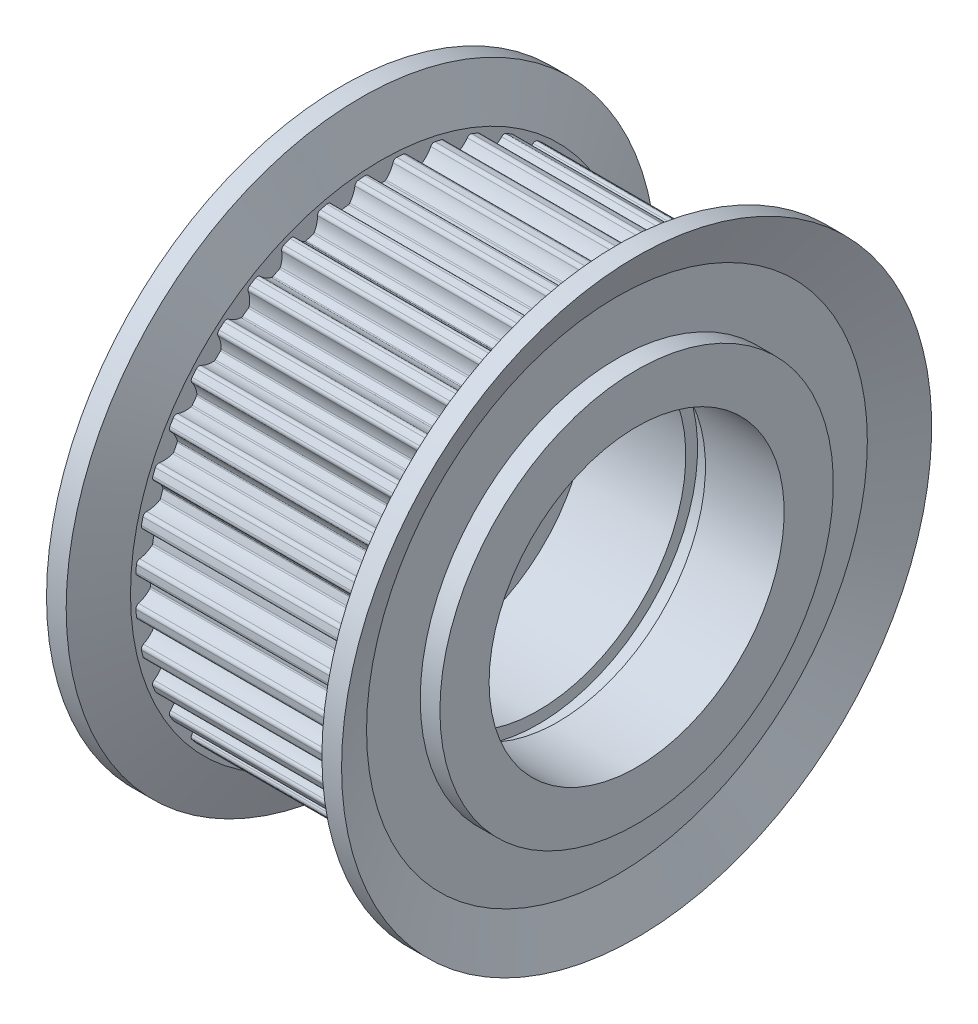
SolidWorks part; units mm, degrees
ref_plane "Front Plane" through (0, 0, 0) normal (0, 0, 1) x (1, 0, 0)
ref_plane "Top Plane" through (0, 0, 0) normal (0, 1, 0) x (1, 0, 0)
ref_plane "Right Plane" through (0, 0, 0) normal (1, 0, 0) x (0, 0, -1)
ref_plane "Plane1" through (0, 0, 0) normal (0, 0, 1) x (1, 0, 0)
sketch "Sketch1" plane through (0, 0, 0) normal (0, 0, 1) x (1, 0, 0)
  line L0 (-7.5, 6.5) -> (-2.5, 6.5)
  line L1 (-2.5, 6.5) -> (-2.5, 7.5)
  line L2 (-2.5, 7.5) -> (2.5, 7.5)
  line L3 (2.5, 7.5) -> (2.5, 8.1)
  line L4 (2.5, 8.1) -> (3.5, 8.1)
  line L5 (3.5, 8.1) -> (3.5, 7.5)
  line L6 (3.5, 7.5) -> (7.5, 7.5)
  line L7 (7.5, 7.5) -> (7.5, 10)
  line L8 (7.5, 10) -> (6.5, 10)
  line L9 (6.5, 10) -> (6.5, 12.73)
  line L10 (6.5, 12.73) -> (7.5, 15)
  line L11 (7.5, 15) -> (6.5, 15)
  line L12 (6.5, 15) -> (5.5, 12.73)
  line L13 (5.5, 12.73) -> (5.5, 12.48)
  line L14 (5.5, 12.48) -> (-5.5, 12.48)
  line L15 (-5.5, 12.48) -> (-5.5, 12.73)
  line L16 (-5.5, 12.73) -> (-6.5, 15)
  line L17 (-6.5, 15) -> (-7.5, 15)
  line L18 (-7.5, 15) -> (-6.5, 12.73)
  line L19 (-6.5, 12.73) -> (-6.5, 10)
  line L20 (-6.5, 10) -> (-7.5, 10)
  line L21 (-7.5, 10) -> (-7.5, 6.5)
  line L22 (15, 0) -> (-15, 0) construction
revolve "Revolve1" add sketch "Sketch1" angle 360 about L22
ref_plane "Plane2" through (5.5, 0, 0) normal (1, 0, 0) x (0, 0, -1)
sketch "Sketch2" plane through (5.5, 0, 0) normal (1, 0, 0) x (0, 0, -1)
  line L0 (0.8092, 12.4537) -> (0.8092, 13.2144)
  line L1 (-0.8092, 13.2144) -> (-0.8092, 12.4537)
  arc A0 (-0.8092, 12.4537) -> (-0.6154, 12.3205) centre (-0.7969, 12.2641) cw
  arc A1 (-0.6154, 12.3205) -> (-0.2549, 11.7455) centre (0.65, 12.7134) ccw
  arc A2 (-0.2549, 11.7455) -> (-0.185, 11.7185) centre (-0.1866, 11.8185) ccw
  arc A3 (-0.185, 11.7185) -> (0.185, 11.7185) centre (0, 0) cw
  arc A4 (0.185, 11.7185) -> (0.2549, 11.7455) centre (0.1866, 11.8185) ccw
  arc A5 (0.2549, 11.7455) -> (0.6154, 12.3205) centre (-0.65, 12.7134) ccw
  arc A6 (0.6154, 12.3205) -> (0.8092, 12.4537) centre (0.7969, 12.2641) cw
  arc A7 (0.8092, 13.2144) -> (-0.8092, 13.2144) centre (0, 0) ccw
extrude "Cut-Extrude1" cut sketch "Sketch2" against normal blind 11
ref_plane "Plane3" through (5.5, 0, 0) normal (1, 0, 0) x (0, 0, -1)
sketch "Sketch3" plane through (5.5, 0, 0) normal (1, 0, 0) x (0, 0, -1)
  line L0 (2.7474, 12.1738) -> (2.8664, 12.9252)
  line L1 (1.268, 13.1783) -> (1.149, 12.427)
  arc A0 (1.149, 12.427) -> (1.3195, 12.2651) centre (1.1315, 12.2378) cw
  arc A1 (1.3195, 12.2651) -> (1.5857, 11.6407) centre (2.6308, 12.4552) ccw
  arc A2 (1.5857, 11.6407) -> (1.6505, 11.6032) centre (1.6646, 11.7022) ccw
  arc A3 (1.6505, 11.6032) -> (2.0159, 11.5453) centre (0, 0) cw
  arc A4 (2.0159, 11.5453) -> (2.0891, 11.561) centre (2.0331, 11.6438) ccw
  arc A5 (2.0891, 11.561) -> (2.5352, 12.0725) centre (1.3468, 12.6586) ccw
  arc A6 (2.5352, 12.0725) -> (2.7474, 12.1738) centre (2.7056, 11.9885) cw
  arc A7 (2.8664, 12.9252) -> (1.268, 13.1783) centre (0, 0) ccw
extrude "Cut-Extrude2" cut sketch "Sketch3" against normal blind 11
ref_plane "Plane4" through (5.5, 0, 0) normal (1, 0, 0) x (0, 0, -1)
sketch "Sketch4" plane through (5.5, 0, 0) normal (1, 0, 0) x (0, 0, -1)
  line L0 (4.618, 11.5942) -> (4.8531, 12.3176)
  line L1 (3.3139, 12.8177) -> (3.0788, 12.0943)
  arc A0 (3.0788, 12.0943) -> (3.222, 11.9076) centre (3.032, 11.9101) cw
  arc A1 (3.222, 11.9076) -> (3.3872, 11.2494) centre (4.5468, 11.8903) ccw
  arc A2 (3.3872, 11.2494) -> (3.4453, 11.2022) centre (3.4747, 11.2977) ccw
  arc A3 (3.4453, 11.2022) -> (3.7972, 11.0878) centre (0, 0) cw
  arc A4 (3.7972, 11.0878) -> (3.8719, 11.0919) centre (3.8296, 11.1824) ccw
  arc A5 (3.8719, 11.0919) -> (4.3925, 11.5273) centre (3.3105, 12.292) ccw
  arc A6 (4.3925, 11.5273) -> (4.618, 11.5942) centre (4.5477, 11.4176) cw
  arc A7 (4.8531, 12.3176) -> (3.3139, 12.8177) centre (0, 0) ccw
extrude "Cut-Extrude3" cut sketch "Sketch4" against normal blind 11
ref_plane "Plane5" through (5.5, 0, 0) normal (1, 0, 0) x (0, 0, -1)
sketch "Sketch5" plane through (5.5, 0, 0) normal (1, 0, 0) x (0, 0, -1)
  line L0 (6.3749, 10.729) -> (6.7202, 11.4068)
  line L1 (5.2783, 12.1415) -> (4.9329, 11.4637)
  arc A0 (4.9329, 11.4637) -> (5.0451, 11.257) centre (4.8578, 11.2892) cw
  arc A1 (5.0451, 11.257) -> (5.1053, 10.581) centre (6.3509, 11.0326) ccw
  arc A2 (5.1053, 10.581) -> (5.1553, 10.5253) centre (5.1993, 10.6151) ccw
  arc A3 (5.1553, 10.5253) -> (5.4849, 10.3573) centre (0, 0) cw
  arc A4 (5.4849, 10.3573) -> (5.5594, 10.3496) centre (5.5317, 10.4457) ccw
  arc A5 (5.5594, 10.3496) -> (6.1417, 10.6982) centre (5.1926, 11.6228) ccw
  arc A6 (6.1417, 10.6982) -> (6.3749, 10.729) centre (6.2778, 10.5657) cw
  arc A7 (6.7202, 11.4068) -> (5.2783, 12.1415) centre (0, 0) ccw
extrude "Cut-Extrude4" cut sketch "Sketch5" against normal blind 11
ref_plane "Plane6" through (5.5, 0, 0) normal (1, 0, 0) x (0, 0, -1)
sketch "Sketch6" plane through (5.5, 0, 0) normal (1, 0, 0) x (0, 0, -1)
  line L0 (7.9748, 9.5997) -> (8.4219, 10.2151)
  line L1 (7.1126, 11.1663) -> (6.6655, 10.5509)
  arc A0 (6.6655, 10.5509) -> (6.7439, 10.3292) centre (6.564, 10.3903) cw
  arc A1 (6.7439, 10.3292) -> (6.6976, 9.6521) centre (7.9986, 9.9033) ccw
  arc A2 (6.6976, 9.6521) -> (6.7383, 9.5892) centre (6.7958, 9.671) ccw
  arc A3 (6.7383, 9.5892) -> (7.0376, 9.3718) centre (0, 0) cw
  arc A4 (7.0376, 9.3718) -> (7.11, 9.3525) centre (7.0977, 9.4517) ccw
  arc A5 (7.11, 9.3525) -> (7.7397, 9.6058) centre (6.9469, 10.6674) ccw
  arc A6 (7.7397, 9.6058) -> (7.9748, 9.5997) centre (7.8534, 9.4535) cw
  arc A7 (8.4219, 10.2151) -> (7.1126, 11.1663) centre (0, 0) ccw
extrude "Cut-Extrude5" cut sketch "Sketch6" against normal blind 11
ref_plane "Plane7" through (5.5, 0, 0) normal (1, 0, 0) x (0, 0, -1)
sketch "Sketch7" plane through (5.5, 0, 0) normal (1, 0, 0) x (0, 0, -1)
  line L0 (9.3783, 8.2339) -> (9.9162, 8.7719)
  line L1 (8.7719, 9.9162) -> (8.2339, 9.3783)
  arc A0 (8.2339, 9.3783) -> (8.2767, 9.1471) centre (8.1086, 9.2355) cw
  arc A1 (8.2767, 9.1471) -> (8.1251, 8.4855) centre (9.4493, 8.5301) ccw
  arc A2 (8.1251, 8.4855) -> (8.1555, 8.4171) centre (8.225, 8.4889) ccw
  arc A3 (8.1555, 8.4171) -> (8.4171, 8.1555) centre (0, 0) cw
  arc A4 (8.4171, 8.1555) -> (8.4855, 8.1251) centre (8.4889, 8.225) ccw
  arc A5 (8.4855, 8.1251) -> (9.1471, 8.2767) centre (8.5301, 9.4493) ccw
  arc A6 (9.1471, 8.2767) -> (9.3783, 8.2339) centre (9.2355, 8.1086) cw
  arc A7 (9.9162, 8.7719) -> (8.7719, 9.9162) centre (0, 0) ccw
extrude "Cut-Extrude6" cut sketch "Sketch7" against normal blind 11
ref_plane "Plane8" through (5.5, 0, 0) normal (1, 0, 0) x (0, 0, -1)
sketch "Sketch8" plane through (5.5, 0, 0) normal (1, 0, 0) x (0, 0, -1)
  line L0 (10.5509, 6.6655) -> (11.1663, 7.1126)
  line L1 (10.2151, 8.4219) -> (9.5997, 7.9748)
  arc A0 (9.5997, 7.9748) -> (9.6058, 7.7397) centre (9.4535, 7.8534) cw
  arc A1 (9.6058, 7.7397) -> (9.3525, 7.11) centre (10.6674, 6.9469) ccw
  arc A2 (9.3525, 7.11) -> (9.3718, 7.0376) centre (9.4517, 7.0977) ccw
  arc A3 (9.3718, 7.0376) -> (9.5892, 6.7383) centre (0, 0) cw
  arc A4 (9.5892, 6.7383) -> (9.6521, 6.6976) centre (9.671, 6.7958) ccw
  arc A5 (9.6521, 6.6976) -> (10.3292, 6.7439) centre (9.9033, 7.9986) ccw
  arc A6 (10.3292, 6.7439) -> (10.5509, 6.6655) centre (10.3903, 6.564) cw
  arc A7 (11.1663, 7.1126) -> (10.2151, 8.4219) centre (0, 0) ccw
extrude "Cut-Extrude7" cut sketch "Sketch8" against normal blind 11
ref_plane "Plane9" through (5.5, 0, 0) normal (1, 0, 0) x (0, 0, -1)
sketch "Sketch9" plane through (5.5, 0, 0) normal (1, 0, 0) x (0, 0, -1)
  line L0 (11.4637, 4.9329) -> (12.1415, 5.2783)
  line L1 (11.4068, 6.7202) -> (10.729, 6.3749)
  arc A0 (10.729, 6.3749) -> (10.6982, 6.1417) centre (10.5657, 6.2778) cw
  arc A1 (10.6982, 6.1417) -> (10.3496, 5.5594) centre (11.6228, 5.1926) ccw
  arc A2 (10.3496, 5.5594) -> (10.3573, 5.4849) centre (10.4457, 5.5317) ccw
  arc A3 (10.3573, 5.4849) -> (10.5253, 5.1553) centre (0, 0) cw
  arc A4 (10.5253, 5.1553) -> (10.581, 5.1053) centre (10.6151, 5.1993) ccw
  arc A5 (10.581, 5.1053) -> (11.257, 5.0451) centre (11.0326, 6.3509) ccw
  arc A6 (11.257, 5.0451) -> (11.4637, 4.9329) centre (11.2892, 4.8578) cw
  arc A7 (12.1415, 5.2783) -> (11.4068, 6.7202) centre (0, 0) ccw
extrude "Cut-Extrude8" cut sketch "Sketch9" against normal blind 11
ref_plane "Plane10" through (5.5, 0, 0) normal (1, 0, 0) x (0, 0, -1)
sketch "Sketch10" plane through (5.5, 0, 0) normal (1, 0, 0) x (0, 0, -1)
  line L0 (12.0943, 3.0788) -> (12.8177, 3.3139)
  line L1 (12.3176, 4.8531) -> (11.5942, 4.618)
  arc A0 (11.5942, 4.618) -> (11.5273, 4.3925) centre (11.4176, 4.5477) cw
  arc A1 (11.5273, 4.3925) -> (11.0919, 3.8719) centre (12.292, 3.3105) ccw
  arc A2 (11.0919, 3.8719) -> (11.0878, 3.7972) centre (11.1824, 3.8296) ccw
  arc A3 (11.0878, 3.7972) -> (11.2022, 3.4453) centre (0, 0) cw
  arc A4 (11.2022, 3.4453) -> (11.2494, 3.3872) centre (11.2977, 3.4747) ccw
  arc A5 (11.2494, 3.3872) -> (11.9076, 3.222) centre (11.8903, 4.5468) ccw
  arc A6 (11.9076, 3.222) -> (12.0943, 3.0788) centre (11.9101, 3.032) cw
  arc A7 (12.8177, 3.3139) -> (12.3176, 4.8531) centre (0, 0) ccw
extrude "Cut-Extrude9" cut sketch "Sketch10" against normal blind 11
ref_plane "Plane11" through (5.5, 0, 0) normal (1, 0, 0) x (0, 0, -1)
sketch "Sketch11" plane through (5.5, 0, 0) normal (1, 0, 0) x (0, 0, -1)
  line L0 (12.427, 1.149) -> (13.1783, 1.268)
  line L1 (12.9252, 2.8664) -> (12.1738, 2.7474)
  arc A0 (12.1738, 2.7474) -> (12.0725, 2.5352) centre (11.9885, 2.7056) cw
  arc A1 (12.0725, 2.5352) -> (11.561, 2.0891) centre (12.6586, 1.3468) ccw
  arc A2 (11.561, 2.0891) -> (11.5453, 2.0159) centre (11.6438, 2.0331) ccw
  arc A3 (11.5453, 2.0159) -> (11.6032, 1.6505) centre (0, 0) cw
  arc A4 (11.6032, 1.6505) -> (11.6407, 1.5857) centre (11.7022, 1.6646) ccw
  arc A5 (11.6407, 1.5857) -> (12.2651, 1.3195) centre (12.4552, 2.6308) ccw
  arc A6 (12.2651, 1.3195) -> (12.427, 1.149) centre (12.2378, 1.1315) cw
  arc A7 (13.1783, 1.268) -> (12.9252, 2.8664) centre (0, 0) ccw
extrude "Cut-Extrude10" cut sketch "Sketch11" against normal blind 11
ref_plane "Plane12" through (5.5, 0, 0) normal (1, 0, 0) x (0, 0, -1)
sketch "Sketch12" plane through (5.5, 0, 0) normal (1, 0, 0) x (0, 0, -1)
  line L0 (12.4537, -0.8092) -> (13.2144, -0.8092)
  line L1 (13.2144, 0.8092) -> (12.4537, 0.8092)
  arc A0 (12.4537, 0.8092) -> (12.3205, 0.6154) centre (12.2641, 0.7969) cw
  arc A1 (12.3205, 0.6154) -> (11.7455, 0.2549) centre (12.7134, -0.65) ccw
  arc A2 (11.7455, 0.2549) -> (11.7185, 0.185) centre (11.8185, 0.1866) ccw
  arc A3 (11.7185, 0.185) -> (11.7185, -0.185) centre (0, 0) cw
  arc A4 (11.7185, -0.185) -> (11.7455, -0.2549) centre (11.8185, -0.1866) ccw
  arc A5 (11.7455, -0.2549) -> (12.3205, -0.6154) centre (12.7134, 0.65) ccw
  arc A6 (12.3205, -0.6154) -> (12.4537, -0.8092) centre (12.2641, -0.7969) cw
  arc A7 (13.2144, -0.8092) -> (13.2144, 0.8092) centre (0, 0) ccw
extrude "Cut-Extrude11" cut sketch "Sketch12" against normal blind 11
ref_plane "Plane13" through (5.5, 0, 0) normal (1, 0, 0) x (0, 0, -1)
sketch "Sketch13" plane through (5.5, 0, 0) normal (1, 0, 0) x (0, 0, -1)
  line L0 (12.1738, -2.7474) -> (12.9252, -2.8664)
  line L1 (13.1783, -1.268) -> (12.427, -1.149)
  arc A0 (12.427, -1.149) -> (12.2651, -1.3195) centre (12.2378, -1.1315) cw
  arc A1 (12.2651, -1.3195) -> (11.6407, -1.5857) centre (12.4552, -2.6308) ccw
  arc A2 (11.6407, -1.5857) -> (11.6032, -1.6505) centre (11.7022, -1.6646) ccw
  arc A3 (11.6032, -1.6505) -> (11.5453, -2.0159) centre (0, 0) cw
  arc A4 (11.5453, -2.0159) -> (11.561, -2.0891) centre (11.6438, -2.0331) ccw
  arc A5 (11.561, -2.0891) -> (12.0725, -2.5352) centre (12.6586, -1.3468) ccw
  arc A6 (12.0725, -2.5352) -> (12.1738, -2.7474) centre (11.9885, -2.7056) cw
  arc A7 (12.9252, -2.8664) -> (13.1783, -1.268) centre (0, 0) ccw
extrude "Cut-Extrude12" cut sketch "Sketch13" against normal blind 11
ref_plane "Plane14" through (5.5, 0, 0) normal (1, 0, 0) x (0, 0, -1)
sketch "Sketch14" plane through (5.5, 0, 0) normal (1, 0, 0) x (0, 0, -1)
  line L0 (11.5942, -4.618) -> (12.3176, -4.8531)
  line L1 (12.8177, -3.3139) -> (12.0943, -3.0788)
  arc A0 (12.0943, -3.0788) -> (11.9076, -3.222) centre (11.9101, -3.032) cw
  arc A1 (11.9076, -3.222) -> (11.2494, -3.3872) centre (11.8903, -4.5468) ccw
  arc A2 (11.2494, -3.3872) -> (11.2022, -3.4453) centre (11.2977, -3.4747) ccw
  arc A3 (11.2022, -3.4453) -> (11.0878, -3.7972) centre (0, 0) cw
  arc A4 (11.0878, -3.7972) -> (11.0919, -3.8719) centre (11.1824, -3.8296) ccw
  arc A5 (11.0919, -3.8719) -> (11.5273, -4.3925) centre (12.292, -3.3105) ccw
  arc A6 (11.5273, -4.3925) -> (11.5942, -4.618) centre (11.4176, -4.5477) cw
  arc A7 (12.3176, -4.8531) -> (12.8177, -3.3139) centre (0, 0) ccw
extrude "Cut-Extrude13" cut sketch "Sketch14" against normal blind 11
ref_plane "Plane15" through (5.5, 0, 0) normal (1, 0, 0) x (0, 0, -1)
sketch "Sketch15" plane through (5.5, 0, 0) normal (1, 0, 0) x (0, 0, -1)
  line L0 (10.729, -6.3749) -> (11.4068, -6.7202)
  line L1 (12.1415, -5.2783) -> (11.4637, -4.9329)
  arc A0 (11.4637, -4.9329) -> (11.257, -5.0451) centre (11.2892, -4.8578) cw
  arc A1 (11.257, -5.0451) -> (10.581, -5.1053) centre (11.0326, -6.3509) ccw
  arc A2 (10.581, -5.1053) -> (10.5253, -5.1553) centre (10.6151, -5.1993) ccw
  arc A3 (10.5253, -5.1553) -> (10.3573, -5.4849) centre (0, 0) cw
  arc A4 (10.3573, -5.4849) -> (10.3496, -5.5594) centre (10.4457, -5.5317) ccw
  arc A5 (10.3496, -5.5594) -> (10.6982, -6.1417) centre (11.6228, -5.1926) ccw
  arc A6 (10.6982, -6.1417) -> (10.729, -6.3749) centre (10.5657, -6.2778) cw
  arc A7 (11.4068, -6.7202) -> (12.1415, -5.2783) centre (0, 0) ccw
extrude "Cut-Extrude14" cut sketch "Sketch15" against normal blind 11
ref_plane "Plane16" through (5.5, 0, 0) normal (1, 0, 0) x (0, 0, -1)
sketch "Sketch16" plane through (5.5, 0, 0) normal (1, 0, 0) x (0, 0, -1)
  line L0 (9.5997, -7.9748) -> (10.2151, -8.4219)
  line L1 (11.1663, -7.1126) -> (10.5509, -6.6655)
  arc A0 (10.5509, -6.6655) -> (10.3292, -6.7439) centre (10.3903, -6.564) cw
  arc A1 (10.3292, -6.7439) -> (9.6521, -6.6976) centre (9.9033, -7.9986) ccw
  arc A2 (9.6521, -6.6976) -> (9.5892, -6.7383) centre (9.671, -6.7958) ccw
  arc A3 (9.5892, -6.7383) -> (9.3718, -7.0376) centre (0, 0) cw
  arc A4 (9.3718, -7.0376) -> (9.3525, -7.11) centre (9.4517, -7.0977) ccw
  arc A5 (9.3525, -7.11) -> (9.6058, -7.7397) centre (10.6674, -6.9469) ccw
  arc A6 (9.6058, -7.7397) -> (9.5997, -7.9748) centre (9.4535, -7.8534) cw
  arc A7 (10.2151, -8.4219) -> (11.1663, -7.1126) centre (0, 0) ccw
extrude "Cut-Extrude15" cut sketch "Sketch16" against normal blind 11
ref_plane "Plane17" through (5.5, 0, 0) normal (1, 0, 0) x (0, 0, -1)
sketch "Sketch17" plane through (5.5, 0, 0) normal (1, 0, 0) x (0, 0, -1)
  line L0 (8.2339, -9.3783) -> (8.7719, -9.9162)
  line L1 (9.9162, -8.7719) -> (9.3783, -8.2339)
  arc A0 (9.3783, -8.2339) -> (9.1471, -8.2767) centre (9.2355, -8.1086) cw
  arc A1 (9.1471, -8.2767) -> (8.4855, -8.1251) centre (8.5301, -9.4493) ccw
  arc A2 (8.4855, -8.1251) -> (8.4171, -8.1555) centre (8.4889, -8.225) ccw
  arc A3 (8.4171, -8.1555) -> (8.1555, -8.4171) centre (0, 0) cw
  arc A4 (8.1555, -8.4171) -> (8.1251, -8.4855) centre (8.225, -8.4889) ccw
  arc A5 (8.1251, -8.4855) -> (8.2767, -9.1471) centre (9.4493, -8.5301) ccw
  arc A6 (8.2767, -9.1471) -> (8.2339, -9.3783) centre (8.1086, -9.2355) cw
  arc A7 (8.7719, -9.9162) -> (9.9162, -8.7719) centre (0, 0) ccw
extrude "Cut-Extrude16" cut sketch "Sketch17" against normal blind 11
ref_plane "Plane18" through (5.5, 0, 0) normal (1, 0, 0) x (0, 0, -1)
sketch "Sketch18" plane through (5.5, 0, 0) normal (1, 0, 0) x (0, 0, -1)
  line L0 (6.6655, -10.5509) -> (7.1126, -11.1663)
  line L1 (8.4219, -10.2151) -> (7.9748, -9.5997)
  arc A0 (7.9748, -9.5997) -> (7.7397, -9.6058) centre (7.8534, -9.4535) cw
  arc A1 (7.7397, -9.6058) -> (7.11, -9.3525) centre (6.9469, -10.6674) ccw
  arc A2 (7.11, -9.3525) -> (7.0376, -9.3718) centre (7.0977, -9.4517) ccw
  arc A3 (7.0376, -9.3718) -> (6.7383, -9.5892) centre (0, 0) cw
  arc A4 (6.7383, -9.5892) -> (6.6976, -9.6521) centre (6.7958, -9.671) ccw
  arc A5 (6.6976, -9.6521) -> (6.7439, -10.3292) centre (7.9986, -9.9033) ccw
  arc A6 (6.7439, -10.3292) -> (6.6655, -10.5509) centre (6.564, -10.3903) cw
  arc A7 (7.1126, -11.1663) -> (8.4219, -10.2151) centre (0, 0) ccw
extrude "Cut-Extrude17" cut sketch "Sketch18" against normal blind 11
ref_plane "Plane19" through (5.5, 0, 0) normal (1, 0, 0) x (0, 0, -1)
sketch "Sketch19" plane through (5.5, 0, 0) normal (1, 0, 0) x (0, 0, -1)
  line L0 (4.9329, -11.4637) -> (5.2783, -12.1415)
  line L1 (6.7202, -11.4068) -> (6.3749, -10.729)
  arc A0 (6.3749, -10.729) -> (6.1417, -10.6982) centre (6.2778, -10.5657) cw
  arc A1 (6.1417, -10.6982) -> (5.5594, -10.3496) centre (5.1926, -11.6228) ccw
  arc A2 (5.5594, -10.3496) -> (5.4849, -10.3573) centre (5.5317, -10.4457) ccw
  arc A3 (5.4849, -10.3573) -> (5.1553, -10.5253) centre (0, 0) cw
  arc A4 (5.1553, -10.5253) -> (5.1053, -10.581) centre (5.1993, -10.6151) ccw
  arc A5 (5.1053, -10.581) -> (5.0451, -11.257) centre (6.3509, -11.0326) ccw
  arc A6 (5.0451, -11.257) -> (4.9329, -11.4637) centre (4.8578, -11.2892) cw
  arc A7 (5.2783, -12.1415) -> (6.7202, -11.4068) centre (0, 0) ccw
extrude "Cut-Extrude18" cut sketch "Sketch19" against normal blind 11
ref_plane "Plane20" through (5.5, 0, 0) normal (1, 0, 0) x (0, 0, -1)
sketch "Sketch20" plane through (5.5, 0, 0) normal (1, 0, 0) x (0, 0, -1)
  line L0 (3.0788, -12.0943) -> (3.3139, -12.8177)
  line L1 (4.8531, -12.3176) -> (4.618, -11.5942)
  arc A0 (4.618, -11.5942) -> (4.3925, -11.5273) centre (4.5477, -11.4176) cw
  arc A1 (4.3925, -11.5273) -> (3.8719, -11.0919) centre (3.3105, -12.292) ccw
  arc A2 (3.8719, -11.0919) -> (3.7972, -11.0878) centre (3.8296, -11.1824) ccw
  arc A3 (3.7972, -11.0878) -> (3.4453, -11.2022) centre (0, 0) cw
  arc A4 (3.4453, -11.2022) -> (3.3872, -11.2494) centre (3.4747, -11.2977) ccw
  arc A5 (3.3872, -11.2494) -> (3.222, -11.9076) centre (4.5468, -11.8903) ccw
  arc A6 (3.222, -11.9076) -> (3.0788, -12.0943) centre (3.032, -11.9101) cw
  arc A7 (3.3139, -12.8177) -> (4.8531, -12.3176) centre (0, 0) ccw
extrude "Cut-Extrude19" cut sketch "Sketch20" against normal blind 11
ref_plane "Plane21" through (5.5, 0, 0) normal (1, 0, 0) x (0, 0, -1)
sketch "Sketch21" plane through (5.5, 0, 0) normal (1, 0, 0) x (0, 0, -1)
  line L0 (1.149, -12.427) -> (1.268, -13.1783)
  line L1 (2.8664, -12.9252) -> (2.7474, -12.1738)
  arc A0 (2.7474, -12.1738) -> (2.5352, -12.0725) centre (2.7056, -11.9885) cw
  arc A1 (2.5352, -12.0725) -> (2.0891, -11.561) centre (1.3468, -12.6586) ccw
  arc A2 (2.0891, -11.561) -> (2.0159, -11.5453) centre (2.0331, -11.6438) ccw
  arc A3 (2.0159, -11.5453) -> (1.6505, -11.6032) centre (0, 0) cw
  arc A4 (1.6505, -11.6032) -> (1.5857, -11.6407) centre (1.6646, -11.7022) ccw
  arc A5 (1.5857, -11.6407) -> (1.3195, -12.2651) centre (2.6308, -12.4552) ccw
  arc A6 (1.3195, -12.2651) -> (1.149, -12.427) centre (1.1315, -12.2378) cw
  arc A7 (1.268, -13.1783) -> (2.8664, -12.9252) centre (0, 0) ccw
extrude "Cut-Extrude20" cut sketch "Sketch21" against normal blind 11
ref_plane "Plane22" through (5.5, 0, 0) normal (1, 0, 0) x (0, 0, -1)
sketch "Sketch22" plane through (5.5, 0, 0) normal (1, 0, 0) x (0, 0, -1)
  line L0 (-0.8092, -12.4537) -> (-0.8092, -13.2144)
  line L1 (0.8092, -13.2144) -> (0.8092, -12.4537)
  arc A0 (0.8092, -12.4537) -> (0.6154, -12.3205) centre (0.7969, -12.2641) cw
  arc A1 (0.6154, -12.3205) -> (0.2549, -11.7455) centre (-0.65, -12.7134) ccw
  arc A2 (0.2549, -11.7455) -> (0.185, -11.7185) centre (0.1866, -11.8185) ccw
  arc A3 (0.185, -11.7185) -> (-0.185, -11.7185) centre (0, 0) cw
  arc A4 (-0.185, -11.7185) -> (-0.2549, -11.7455) centre (-0.1866, -11.8185) ccw
  arc A5 (-0.2549, -11.7455) -> (-0.6154, -12.3205) centre (0.65, -12.7134) ccw
  arc A6 (-0.6154, -12.3205) -> (-0.8092, -12.4537) centre (-0.7969, -12.2641) cw
  arc A7 (-0.8092, -13.2144) -> (0.8092, -13.2144) centre (0, 0) ccw
extrude "Cut-Extrude21" cut sketch "Sketch22" against normal blind 11
ref_plane "Plane23" through (5.5, 0, 0) normal (1, 0, 0) x (0, 0, -1)
sketch "Sketch23" plane through (5.5, 0, 0) normal (1, 0, 0) x (0, 0, -1)
  line L0 (-2.7474, -12.1738) -> (-2.8664, -12.9252)
  line L1 (-1.268, -13.1783) -> (-1.149, -12.427)
  arc A0 (-1.149, -12.427) -> (-1.3195, -12.2651) centre (-1.1315, -12.2378) cw
  arc A1 (-1.3195, -12.2651) -> (-1.5857, -11.6407) centre (-2.6308, -12.4552) ccw
  arc A2 (-1.5857, -11.6407) -> (-1.6505, -11.6032) centre (-1.6646, -11.7022) ccw
  arc A3 (-1.6505, -11.6032) -> (-2.0159, -11.5453) centre (0, 0) cw
  arc A4 (-2.0159, -11.5453) -> (-2.0891, -11.561) centre (-2.0331, -11.6438) ccw
  arc A5 (-2.0891, -11.561) -> (-2.5352, -12.0725) centre (-1.3468, -12.6586) ccw
  arc A6 (-2.5352, -12.0725) -> (-2.7474, -12.1738) centre (-2.7056, -11.9885) cw
  arc A7 (-2.8664, -12.9252) -> (-1.268, -13.1783) centre (0, 0) ccw
extrude "Cut-Extrude22" cut sketch "Sketch23" against normal blind 11
ref_plane "Plane24" through (5.5, 0, 0) normal (1, 0, 0) x (0, 0, -1)
sketch "Sketch24" plane through (5.5, 0, 0) normal (1, 0, 0) x (0, 0, -1)
  line L0 (-4.618, -11.5942) -> (-4.8531, -12.3176)
  line L1 (-3.3139, -12.8177) -> (-3.0788, -12.0943)
  arc A0 (-3.0788, -12.0943) -> (-3.222, -11.9076) centre (-3.032, -11.9101) cw
  arc A1 (-3.222, -11.9076) -> (-3.3872, -11.2494) centre (-4.5468, -11.8903) ccw
  arc A2 (-3.3872, -11.2494) -> (-3.4453, -11.2022) centre (-3.4747, -11.2977) ccw
  arc A3 (-3.4453, -11.2022) -> (-3.7972, -11.0878) centre (0, 0) cw
  arc A4 (-3.7972, -11.0878) -> (-3.8719, -11.0919) centre (-3.8296, -11.1824) ccw
  arc A5 (-3.8719, -11.0919) -> (-4.3925, -11.5273) centre (-3.3105, -12.292) ccw
  arc A6 (-4.3925, -11.5273) -> (-4.618, -11.5942) centre (-4.5477, -11.4176) cw
  arc A7 (-4.8531, -12.3176) -> (-3.3139, -12.8177) centre (0, 0) ccw
extrude "Cut-Extrude23" cut sketch "Sketch24" against normal blind 11
ref_plane "Plane25" through (5.5, 0, 0) normal (1, 0, 0) x (0, 0, -1)
sketch "Sketch25" plane through (5.5, 0, 0) normal (1, 0, 0) x (0, 0, -1)
  line L0 (-6.3749, -10.729) -> (-6.7202, -11.4068)
  line L1 (-5.2783, -12.1415) -> (-4.9329, -11.4637)
  arc A0 (-4.9329, -11.4637) -> (-5.0451, -11.257) centre (-4.8578, -11.2892) cw
  arc A1 (-5.0451, -11.257) -> (-5.1053, -10.581) centre (-6.3509, -11.0326) ccw
  arc A2 (-5.1053, -10.581) -> (-5.1553, -10.5253) centre (-5.1993, -10.6151) ccw
  arc A3 (-5.1553, -10.5253) -> (-5.4849, -10.3573) centre (0, 0) cw
  arc A4 (-5.4849, -10.3573) -> (-5.5594, -10.3496) centre (-5.5317, -10.4457) ccw
  arc A5 (-5.5594, -10.3496) -> (-6.1417, -10.6982) centre (-5.1926, -11.6228) ccw
  arc A6 (-6.1417, -10.6982) -> (-6.3749, -10.729) centre (-6.2778, -10.5657) cw
  arc A7 (-6.7202, -11.4068) -> (-5.2783, -12.1415) centre (0, 0) ccw
extrude "Cut-Extrude24" cut sketch "Sketch25" against normal blind 11
ref_plane "Plane26" through (5.5, 0, 0) normal (1, 0, 0) x (0, 0, -1)
sketch "Sketch26" plane through (5.5, 0, 0) normal (1, 0, 0) x (0, 0, -1)
  line L0 (-7.9748, -9.5997) -> (-8.4219, -10.2151)
  line L1 (-7.1126, -11.1663) -> (-6.6655, -10.5509)
  arc A0 (-6.6655, -10.5509) -> (-6.7439, -10.3292) centre (-6.564, -10.3903) cw
  arc A1 (-6.7439, -10.3292) -> (-6.6976, -9.6521) centre (-7.9986, -9.9033) ccw
  arc A2 (-6.6976, -9.6521) -> (-6.7383, -9.5892) centre (-6.7958, -9.671) ccw
  arc A3 (-6.7383, -9.5892) -> (-7.0376, -9.3718) centre (0, 0) cw
  arc A4 (-7.0376, -9.3718) -> (-7.11, -9.3525) centre (-7.0977, -9.4517) ccw
  arc A5 (-7.11, -9.3525) -> (-7.7397, -9.6058) centre (-6.9469, -10.6674) ccw
  arc A6 (-7.7397, -9.6058) -> (-7.9748, -9.5997) centre (-7.8534, -9.4535) cw
  arc A7 (-8.4219, -10.2151) -> (-7.1126, -11.1663) centre (0, 0) ccw
extrude "Cut-Extrude25" cut sketch "Sketch26" against normal blind 11
ref_plane "Plane27" through (5.5, 0, 0) normal (1, 0, 0) x (0, 0, -1)
sketch "Sketch27" plane through (5.5, 0, 0) normal (1, 0, 0) x (0, 0, -1)
  line L0 (-9.3783, -8.2339) -> (-9.9162, -8.7719)
  line L1 (-8.7719, -9.9162) -> (-8.2339, -9.3783)
  arc A0 (-8.2339, -9.3783) -> (-8.2767, -9.1471) centre (-8.1086, -9.2355) cw
  arc A1 (-8.2767, -9.1471) -> (-8.1251, -8.4855) centre (-9.4493, -8.5301) ccw
  arc A2 (-8.1251, -8.4855) -> (-8.1555, -8.4171) centre (-8.225, -8.4889) ccw
  arc A3 (-8.1555, -8.4171) -> (-8.4171, -8.1555) centre (0, 0) cw
  arc A4 (-8.4171, -8.1555) -> (-8.4855, -8.1251) centre (-8.4889, -8.225) ccw
  arc A5 (-8.4855, -8.1251) -> (-9.1471, -8.2767) centre (-8.5301, -9.4493) ccw
  arc A6 (-9.1471, -8.2767) -> (-9.3783, -8.2339) centre (-9.2355, -8.1086) cw
  arc A7 (-9.9162, -8.7719) -> (-8.7719, -9.9162) centre (0, 0) ccw
extrude "Cut-Extrude26" cut sketch "Sketch27" against normal blind 11
ref_plane "Plane28" through (5.5, 0, 0) normal (1, 0, 0) x (0, 0, -1)
sketch "Sketch28" plane through (5.5, 0, 0) normal (1, 0, 0) x (0, 0, -1)
  line L0 (-10.5509, -6.6655) -> (-11.1663, -7.1126)
  line L1 (-10.2151, -8.4219) -> (-9.5997, -7.9748)
  arc A0 (-9.5997, -7.9748) -> (-9.6058, -7.7397) centre (-9.4535, -7.8534) cw
  arc A1 (-9.6058, -7.7397) -> (-9.3525, -7.11) centre (-10.6674, -6.9469) ccw
  arc A2 (-9.3525, -7.11) -> (-9.3718, -7.0376) centre (-9.4517, -7.0977) ccw
  arc A3 (-9.3718, -7.0376) -> (-9.5892, -6.7383) centre (0, 0) cw
  arc A4 (-9.5892, -6.7383) -> (-9.6521, -6.6976) centre (-9.671, -6.7958) ccw
  arc A5 (-9.6521, -6.6976) -> (-10.3292, -6.7439) centre (-9.9033, -7.9986) ccw
  arc A6 (-10.3292, -6.7439) -> (-10.5509, -6.6655) centre (-10.3903, -6.564) cw
  arc A7 (-11.1663, -7.1126) -> (-10.2151, -8.4219) centre (0, 0) ccw
extrude "Cut-Extrude27" cut sketch "Sketch28" against normal blind 11
ref_plane "Plane29" through (5.5, 0, 0) normal (1, 0, 0) x (0, 0, -1)
sketch "Sketch29" plane through (5.5, 0, 0) normal (1, 0, 0) x (0, 0, -1)
  line L0 (-11.4637, -4.9329) -> (-12.1415, -5.2783)
  line L1 (-11.4068, -6.7202) -> (-10.729, -6.3749)
  arc A0 (-10.729, -6.3749) -> (-10.6982, -6.1417) centre (-10.5657, -6.2778) cw
  arc A1 (-10.6982, -6.1417) -> (-10.3496, -5.5594) centre (-11.6228, -5.1926) ccw
  arc A2 (-10.3496, -5.5594) -> (-10.3573, -5.4849) centre (-10.4457, -5.5317) ccw
  arc A3 (-10.3573, -5.4849) -> (-10.5253, -5.1553) centre (0, 0) cw
  arc A4 (-10.5253, -5.1553) -> (-10.581, -5.1053) centre (-10.6151, -5.1993) ccw
  arc A5 (-10.581, -5.1053) -> (-11.257, -5.0451) centre (-11.0326, -6.3509) ccw
  arc A6 (-11.257, -5.0451) -> (-11.4637, -4.9329) centre (-11.2892, -4.8578) cw
  arc A7 (-12.1415, -5.2783) -> (-11.4068, -6.7202) centre (0, 0) ccw
extrude "Cut-Extrude28" cut sketch "Sketch29" against normal blind 11
ref_plane "Plane30" through (5.5, 0, 0) normal (1, 0, 0) x (0, 0, -1)
sketch "Sketch30" plane through (5.5, 0, 0) normal (1, 0, 0) x (0, 0, -1)
  line L0 (-12.0943, -3.0788) -> (-12.8177, -3.3139)
  line L1 (-12.3176, -4.8531) -> (-11.5942, -4.618)
  arc A0 (-11.5942, -4.618) -> (-11.5273, -4.3925) centre (-11.4176, -4.5477) cw
  arc A1 (-11.5273, -4.3925) -> (-11.0919, -3.8719) centre (-12.292, -3.3105) ccw
  arc A2 (-11.0919, -3.8719) -> (-11.0878, -3.7972) centre (-11.1824, -3.8296) ccw
  arc A3 (-11.0878, -3.7972) -> (-11.2022, -3.4453) centre (0, 0) cw
  arc A4 (-11.2022, -3.4453) -> (-11.2494, -3.3872) centre (-11.2977, -3.4747) ccw
  arc A5 (-11.2494, -3.3872) -> (-11.9076, -3.222) centre (-11.8903, -4.5468) ccw
  arc A6 (-11.9076, -3.222) -> (-12.0943, -3.0788) centre (-11.9101, -3.032) cw
  arc A7 (-12.8177, -3.3139) -> (-12.3176, -4.8531) centre (0, 0) ccw
extrude "Cut-Extrude29" cut sketch "Sketch30" against normal blind 11
ref_plane "Plane31" through (5.5, 0, 0) normal (1, 0, 0) x (0, 0, -1)
sketch "Sketch31" plane through (5.5, 0, 0) normal (1, 0, 0) x (0, 0, -1)
  line L0 (-12.427, -1.149) -> (-13.1783, -1.268)
  line L1 (-12.9252, -2.8664) -> (-12.1738, -2.7474)
  arc A0 (-12.1738, -2.7474) -> (-12.0725, -2.5352) centre (-11.9885, -2.7056) cw
  arc A1 (-12.0725, -2.5352) -> (-11.561, -2.0891) centre (-12.6586, -1.3468) ccw
  arc A2 (-11.561, -2.0891) -> (-11.5453, -2.0159) centre (-11.6438, -2.0331) ccw
  arc A3 (-11.5453, -2.0159) -> (-11.6032, -1.6505) centre (0, 0) cw
  arc A4 (-11.6032, -1.6505) -> (-11.6407, -1.5857) centre (-11.7022, -1.6646) ccw
  arc A5 (-11.6407, -1.5857) -> (-12.2651, -1.3195) centre (-12.4552, -2.6308) ccw
  arc A6 (-12.2651, -1.3195) -> (-12.427, -1.149) centre (-12.2378, -1.1315) cw
  arc A7 (-13.1783, -1.268) -> (-12.9252, -2.8664) centre (0, 0) ccw
extrude "Cut-Extrude30" cut sketch "Sketch31" against normal blind 11
ref_plane "Plane32" through (5.5, 0, 0) normal (1, 0, 0) x (0, 0, -1)
sketch "Sketch32" plane through (5.5, 0, 0) normal (1, 0, 0) x (0, 0, -1)
  line L0 (-12.4537, 0.8092) -> (-13.2144, 0.8092)
  line L1 (-13.2144, -0.8092) -> (-12.4537, -0.8092)
  arc A0 (-12.4537, -0.8092) -> (-12.3205, -0.6154) centre (-12.2641, -0.7969) cw
  arc A1 (-12.3205, -0.6154) -> (-11.7455, -0.2549) centre (-12.7134, 0.65) ccw
  arc A2 (-11.7455, -0.2549) -> (-11.7185, -0.185) centre (-11.8185, -0.1866) ccw
  arc A3 (-11.7185, -0.185) -> (-11.7185, 0.185) centre (0, 0) cw
  arc A4 (-11.7185, 0.185) -> (-11.7455, 0.2549) centre (-11.8185, 0.1866) ccw
  arc A5 (-11.7455, 0.2549) -> (-12.3205, 0.6154) centre (-12.7134, -0.65) ccw
  arc A6 (-12.3205, 0.6154) -> (-12.4537, 0.8092) centre (-12.2641, 0.7969) cw
  arc A7 (-13.2144, 0.8092) -> (-13.2144, -0.8092) centre (0, 0) ccw
extrude "Cut-Extrude31" cut sketch "Sketch32" against normal blind 11
ref_plane "Plane33" through (5.5, 0, 0) normal (1, 0, 0) x (0, 0, -1)
sketch "Sketch33" plane through (5.5, 0, 0) normal (1, 0, 0) x (0, 0, -1)
  line L0 (-12.1738, 2.7474) -> (-12.9252, 2.8664)
  line L1 (-13.1783, 1.268) -> (-12.427, 1.149)
  arc A0 (-12.427, 1.149) -> (-12.2651, 1.3195) centre (-12.2378, 1.1315) cw
  arc A1 (-12.2651, 1.3195) -> (-11.6407, 1.5857) centre (-12.4552, 2.6308) ccw
  arc A2 (-11.6407, 1.5857) -> (-11.6032, 1.6505) centre (-11.7022, 1.6646) ccw
  arc A3 (-11.6032, 1.6505) -> (-11.5453, 2.0159) centre (0, 0) cw
  arc A4 (-11.5453, 2.0159) -> (-11.561, 2.0891) centre (-11.6438, 2.0331) ccw
  arc A5 (-11.561, 2.0891) -> (-12.0725, 2.5352) centre (-12.6586, 1.3468) ccw
  arc A6 (-12.0725, 2.5352) -> (-12.1738, 2.7474) centre (-11.9885, 2.7056) cw
  arc A7 (-12.9252, 2.8664) -> (-13.1783, 1.268) centre (0, 0) ccw
extrude "Cut-Extrude32" cut sketch "Sketch33" against normal blind 11
ref_plane "Plane34" through (5.5, 0, 0) normal (1, 0, 0) x (0, 0, -1)
sketch "Sketch34" plane through (5.5, 0, 0) normal (1, 0, 0) x (0, 0, -1)
  line L0 (-11.5942, 4.618) -> (-12.3176, 4.8531)
  line L1 (-12.8177, 3.3139) -> (-12.0943, 3.0788)
  arc A0 (-12.0943, 3.0788) -> (-11.9076, 3.222) centre (-11.9101, 3.032) cw
  arc A1 (-11.9076, 3.222) -> (-11.2494, 3.3872) centre (-11.8903, 4.5468) ccw
  arc A2 (-11.2494, 3.3872) -> (-11.2022, 3.4453) centre (-11.2977, 3.4747) ccw
  arc A3 (-11.2022, 3.4453) -> (-11.0878, 3.7972) centre (0, 0) cw
  arc A4 (-11.0878, 3.7972) -> (-11.0919, 3.8719) centre (-11.1824, 3.8296) ccw
  arc A5 (-11.0919, 3.8719) -> (-11.5273, 4.3925) centre (-12.292, 3.3105) ccw
  arc A6 (-11.5273, 4.3925) -> (-11.5942, 4.618) centre (-11.4176, 4.5477) cw
  arc A7 (-12.3176, 4.8531) -> (-12.8177, 3.3139) centre (0, 0) ccw
extrude "Cut-Extrude33" cut sketch "Sketch34" against normal blind 11
ref_plane "Plane35" through (5.5, 0, 0) normal (1, 0, 0) x (0, 0, -1)
sketch "Sketch35" plane through (5.5, 0, 0) normal (1, 0, 0) x (0, 0, -1)
  line L0 (-10.729, 6.3749) -> (-11.4068, 6.7202)
  line L1 (-12.1415, 5.2783) -> (-11.4637, 4.9329)
  arc A0 (-11.4637, 4.9329) -> (-11.257, 5.0451) centre (-11.2892, 4.8578) cw
  arc A1 (-11.257, 5.0451) -> (-10.581, 5.1053) centre (-11.0326, 6.3509) ccw
  arc A2 (-10.581, 5.1053) -> (-10.5253, 5.1553) centre (-10.6151, 5.1993) ccw
  arc A3 (-10.5253, 5.1553) -> (-10.3573, 5.4849) centre (0, 0) cw
  arc A4 (-10.3573, 5.4849) -> (-10.3496, 5.5594) centre (-10.4457, 5.5317) ccw
  arc A5 (-10.3496, 5.5594) -> (-10.6982, 6.1417) centre (-11.6228, 5.1926) ccw
  arc A6 (-10.6982, 6.1417) -> (-10.729, 6.3749) centre (-10.5657, 6.2778) cw
  arc A7 (-11.4068, 6.7202) -> (-12.1415, 5.2783) centre (0, 0) ccw
extrude "Cut-Extrude34" cut sketch "Sketch35" against normal blind 11
ref_plane "Plane36" through (5.5, 0, 0) normal (1, 0, 0) x (0, 0, -1)
sketch "Sketch36" plane through (5.5, 0, 0) normal (1, 0, 0) x (0, 0, -1)
  line L0 (-9.5997, 7.9748) -> (-10.2151, 8.4219)
  line L1 (-11.1663, 7.1126) -> (-10.5509, 6.6655)
  arc A0 (-10.5509, 6.6655) -> (-10.3292, 6.7439) centre (-10.3903, 6.564) cw
  arc A1 (-10.3292, 6.7439) -> (-9.6521, 6.6976) centre (-9.9033, 7.9986) ccw
  arc A2 (-9.6521, 6.6976) -> (-9.5892, 6.7383) centre (-9.671, 6.7958) ccw
  arc A3 (-9.5892, 6.7383) -> (-9.3718, 7.0376) centre (0, 0) cw
  arc A4 (-9.3718, 7.0376) -> (-9.3525, 7.11) centre (-9.4517, 7.0977) ccw
  arc A5 (-9.3525, 7.11) -> (-9.6058, 7.7397) centre (-10.6674, 6.9469) ccw
  arc A6 (-9.6058, 7.7397) -> (-9.5997, 7.9748) centre (-9.4535, 7.8534) cw
  arc A7 (-10.2151, 8.4219) -> (-11.1663, 7.1126) centre (0, 0) ccw
extrude "Cut-Extrude35" cut sketch "Sketch36" against normal blind 11
ref_plane "Plane37" through (5.5, 0, 0) normal (1, 0, 0) x (0, 0, -1)
sketch "Sketch37" plane through (5.5, 0, 0) normal (1, 0, 0) x (0, 0, -1)
  line L0 (-8.2339, 9.3783) -> (-8.7719, 9.9162)
  line L1 (-9.9162, 8.7719) -> (-9.3783, 8.2339)
  arc A0 (-9.3783, 8.2339) -> (-9.1471, 8.2767) centre (-9.2355, 8.1086) cw
  arc A1 (-9.1471, 8.2767) -> (-8.4855, 8.1251) centre (-8.5301, 9.4493) ccw
  arc A2 (-8.4855, 8.1251) -> (-8.4171, 8.1555) centre (-8.4889, 8.225) ccw
  arc A3 (-8.4171, 8.1555) -> (-8.1555, 8.4171) centre (0, 0) cw
  arc A4 (-8.1555, 8.4171) -> (-8.1251, 8.4855) centre (-8.225, 8.4889) ccw
  arc A5 (-8.1251, 8.4855) -> (-8.2767, 9.1471) centre (-9.4493, 8.5301) ccw
  arc A6 (-8.2767, 9.1471) -> (-8.2339, 9.3783) centre (-8.1086, 9.2355) cw
  arc A7 (-8.7719, 9.9162) -> (-9.9162, 8.7719) centre (0, 0) ccw
extrude "Cut-Extrude36" cut sketch "Sketch37" against normal blind 11
ref_plane "Plane38" through (5.5, 0, 0) normal (1, 0, 0) x (0, 0, -1)
sketch "Sketch38" plane through (5.5, 0, 0) normal (1, 0, 0) x (0, 0, -1)
  line L0 (-6.6655, 10.5509) -> (-7.1126, 11.1663)
  line L1 (-8.4219, 10.2151) -> (-7.9748, 9.5997)
  arc A0 (-7.9748, 9.5997) -> (-7.7397, 9.6058) centre (-7.8534, 9.4535) cw
  arc A1 (-7.7397, 9.6058) -> (-7.11, 9.3525) centre (-6.9469, 10.6674) ccw
  arc A2 (-7.11, 9.3525) -> (-7.0376, 9.3718) centre (-7.0977, 9.4517) ccw
  arc A3 (-7.0376, 9.3718) -> (-6.7383, 9.5892) centre (0, 0) cw
  arc A4 (-6.7383, 9.5892) -> (-6.6976, 9.6521) centre (-6.7958, 9.671) ccw
  arc A5 (-6.6976, 9.6521) -> (-6.7439, 10.3292) centre (-7.9986, 9.9033) ccw
  arc A6 (-6.7439, 10.3292) -> (-6.6655, 10.5509) centre (-6.564, 10.3903) cw
  arc A7 (-7.1126, 11.1663) -> (-8.4219, 10.2151) centre (0, 0) ccw
extrude "Cut-Extrude37" cut sketch "Sketch38" against normal blind 11
ref_plane "Plane39" through (5.5, 0, 0) normal (1, 0, 0) x (0, 0, -1)
sketch "Sketch39" plane through (5.5, 0, 0) normal (1, 0, 0) x (0, 0, -1)
  line L0 (-4.9329, 11.4637) -> (-5.2783, 12.1415)
  line L1 (-6.7202, 11.4068) -> (-6.3749, 10.729)
  arc A0 (-6.3749, 10.729) -> (-6.1417, 10.6982) centre (-6.2778, 10.5657) cw
  arc A1 (-6.1417, 10.6982) -> (-5.5594, 10.3496) centre (-5.1926, 11.6228) ccw
  arc A2 (-5.5594, 10.3496) -> (-5.4849, 10.3573) centre (-5.5317, 10.4457) ccw
  arc A3 (-5.4849, 10.3573) -> (-5.1553, 10.5253) centre (0, 0) cw
  arc A4 (-5.1553, 10.5253) -> (-5.1053, 10.581) centre (-5.1993, 10.6151) ccw
  arc A5 (-5.1053, 10.581) -> (-5.0451, 11.257) centre (-6.3509, 11.0326) ccw
  arc A6 (-5.0451, 11.257) -> (-4.9329, 11.4637) centre (-4.8578, 11.2892) cw
  arc A7 (-5.2783, 12.1415) -> (-6.7202, 11.4068) centre (0, 0) ccw
extrude "Cut-Extrude38" cut sketch "Sketch39" against normal blind 11
ref_plane "Plane40" through (5.5, 0, 0) normal (1, 0, 0) x (0, 0, -1)
sketch "Sketch40" plane through (5.5, 0, 0) normal (1, 0, 0) x (0, 0, -1)
  line L0 (-3.0788, 12.0943) -> (-3.3139, 12.8177)
  line L1 (-4.8531, 12.3176) -> (-4.618, 11.5942)
  arc A0 (-4.618, 11.5942) -> (-4.3925, 11.5273) centre (-4.5477, 11.4176) cw
  arc A1 (-4.3925, 11.5273) -> (-3.8719, 11.0919) centre (-3.3105, 12.292) ccw
  arc A2 (-3.8719, 11.0919) -> (-3.7972, 11.0878) centre (-3.8296, 11.1824) ccw
  arc A3 (-3.7972, 11.0878) -> (-3.4453, 11.2022) centre (0, 0) cw
  arc A4 (-3.4453, 11.2022) -> (-3.3872, 11.2494) centre (-3.4747, 11.2977) ccw
  arc A5 (-3.3872, 11.2494) -> (-3.222, 11.9076) centre (-4.5468, 11.8903) ccw
  arc A6 (-3.222, 11.9076) -> (-3.0788, 12.0943) centre (-3.032, 11.9101) cw
  arc A7 (-3.3139, 12.8177) -> (-4.8531, 12.3176) centre (0, 0) ccw
extrude "Cut-Extrude39" cut sketch "Sketch40" against normal blind 11
ref_plane "Plane41" through (5.5, 0, 0) normal (1, 0, 0) x (0, 0, -1)
sketch "Sketch41" plane through (5.5, 0, 0) normal (1, 0, 0) x (0, 0, -1)
  line L0 (-1.149, 12.427) -> (-1.268, 13.1783)
  line L1 (-2.8664, 12.9252) -> (-2.7474, 12.1738)
  arc A0 (-2.7474, 12.1738) -> (-2.5352, 12.0725) centre (-2.7056, 11.9885) cw
  arc A1 (-2.5352, 12.0725) -> (-2.0891, 11.561) centre (-1.3468, 12.6586) ccw
  arc A2 (-2.0891, 11.561) -> (-2.0159, 11.5453) centre (-2.0331, 11.6438) ccw
  arc A3 (-2.0159, 11.5453) -> (-1.6505, 11.6032) centre (0, 0) cw
  arc A4 (-1.6505, 11.6032) -> (-1.5857, 11.6407) centre (-1.6646, 11.7022) ccw
  arc A5 (-1.5857, 11.6407) -> (-1.3195, 12.2651) centre (-2.6308, 12.4552) ccw
  arc A6 (-1.3195, 12.2651) -> (-1.149, 12.427) centre (-1.1315, 12.2378) cw
  arc A7 (-1.268, 13.1783) -> (-2.8664, 12.9252) centre (0, 0) ccw
extrude "Cut-Extrude40" cut sketch "Sketch41" against normal blind 11
